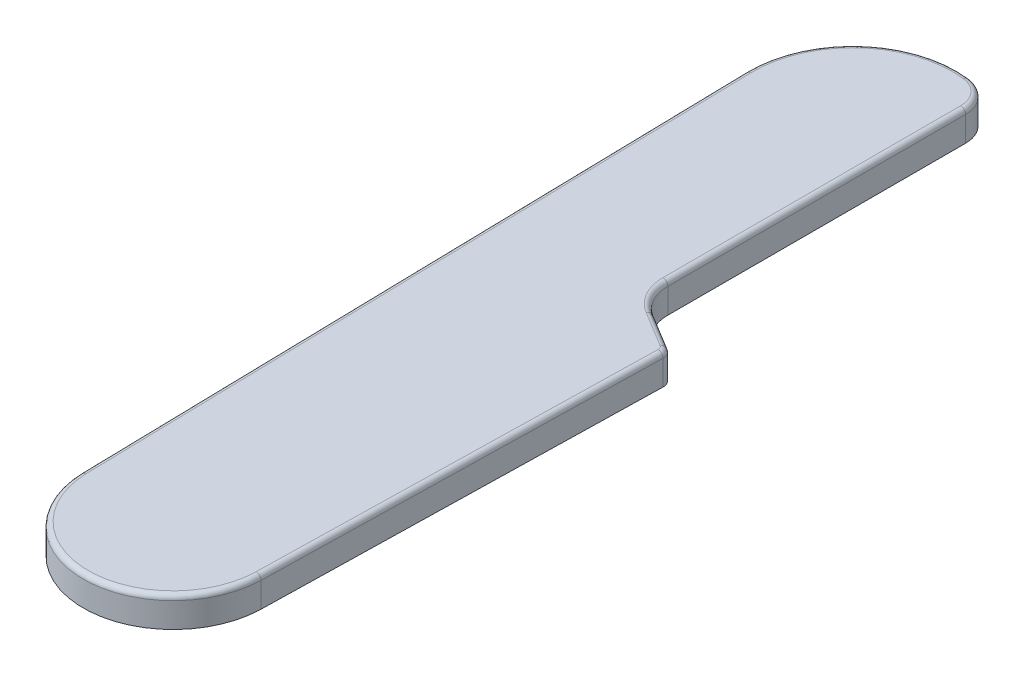
SolidWorks part; units mm, degrees
material "1060 Alloy"
ref_plane "Front Plane" through (0, 0, 0) normal (0, 0, 1) x (1, 0, 0)
ref_plane "Top Plane" through (0, 0, 0) normal (0, 1, 0) x (1, 0, 0)
ref_plane "Right Plane" through (0, 0, 0) normal (1, 0, 0) x (0, 0, -1)
sketch "cover_itself" plane through (0, 0, 0) normal (0, 1, 0) x (1, 0, 0)
  line L0 (-8.9979, -0.1963) -> (-10.4809, 67.7713)
  line L1 (3.8693, 77.7432) -> (3.8693, 43.3841)
  line L2 (3.8693, 43.3841) -> (9.8693, 39.7432)
  line L3 (9.8693, 39.7432) -> (8.9979, -0.1963)
  line L4 (0, -9) -> (0, 93.5367) construction
  arc A0 (-8.9979, -0.1963) -> (8.9979, -0.1963) centre (0, 0) ccw
  arc A1 (-10.4809, 67.7713) -> (3.8693, 77.7432) centre (0, 68) cw
  dimension "D1" = 9
  dimension "D2" = 68
  dimension "D3" = 38
  dimension "D4" = 120
  dimension "D5" = 2.5
  dimension "D6" = 6
extrude "Boss-Extrude1" add sketch "cover_itself" along normal blind 3
fillet "Fillet1" radius 4 1 edges at (3.8693, 1.5, -43.3841)
fillet "Fillet2" radius 3 1 edges at (3.8693, 1.5, -77.7432)
fillet "Fillet3" radius 1 1 edges at (9.8693, 1.5, -39.7432)
fillet "Fillet5" radius 0.5 9 edges at (0, 3, 9) (-9.7394, 3, -33.7875) (-7.054, 3, -75.7552) (3.1105, 3, -77.427) (3.8693, 3, -60.5342) (4.3836, 3, -43.6736) (7.585, 3, -41.1294) (9.7337, 3, -39.6688) (9.4273, 3, -19.4848)
sketch "Sketch1" plane through (0, 0, 0) normal (0, -1, 0) x (1, 0, 0)
  line L0 (-2.1816, 11.5327) -> (-5.8603, -81.249) construction
  line L1 (8.9979, 0.1963) -> (9.8567, -39.166) construction
  circle A0 centre (-2.7051, -1.67) radius 1
  circle A1 centre (6.7698, -35.216) radius 1
  circle A2 centre (-5.3991, -69.6166) radius 1
  dimension "D2" = 2
  dimension "D1" = 2.6368
  dimension "D3" = 1.67
  dimension "D4" = 68
  dimension "D5" = 7
  dimension "D6" = 3
extrude "Cut-Extrude1" cut sketch "Sketch1" against normal blind 2
